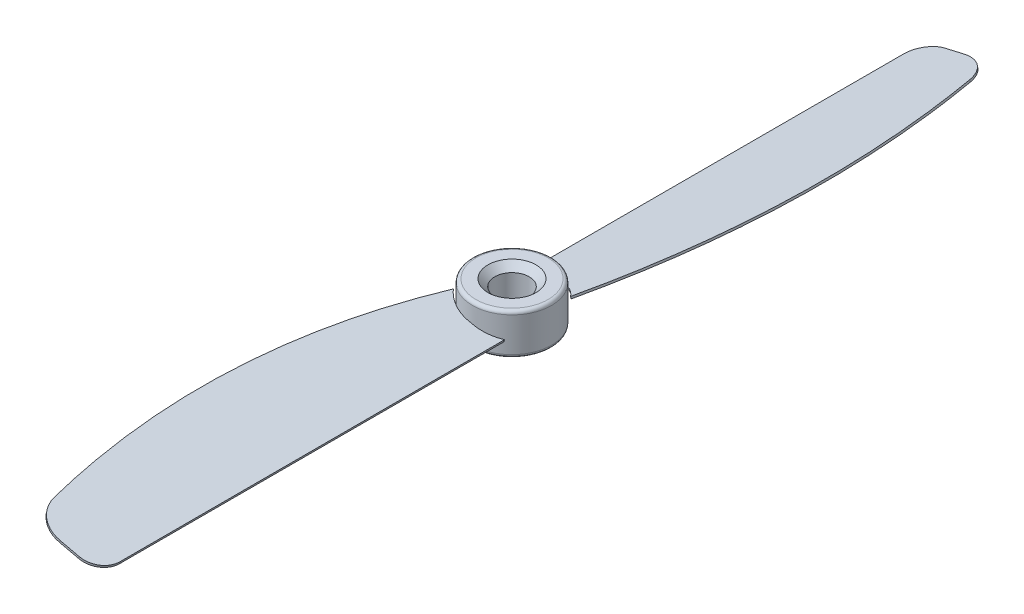
SolidWorks part; units mm, degrees
ref_plane "Front Plane" through (0, 0, 0) normal (0, 0, 1) x (1, 0, 0)
ref_plane "Top Plane" through (0, 0, 0) normal (0, 1, 0) x (1, 0, 0)
ref_plane "Right Plane" through (0, 0, 0) normal (1, 0, 0) x (0, 0, -1)
sketch "Sketch1" plane through (0, 0, 0) normal (0, 1, 0) x (1, 0, 0)
  circle A0 centre (0, 0) radius 5.75
  dimension "D1" = 11.5
extrude "Boss-Extrude1" add sketch "Sketch1" along normal mid plane 6
sketch "Sketch2" plane through (0, 0, 0) normal (0, 0, 1) x (1, 0, 0)
  line L0 (-5.75, 1.3275) -> (5.75, -1.3275) construction
  line L1 (-5.75, 3) -> (-5.75, -3) construction
  line L2 (5.75, -3) -> (5.75, 3) construction
  line L3 (-5.75, -3) -> (5.75, -3) construction
  dimension "D1" = 13
ref_plane "Plane1" through (0, 0, 0) normal (-0.225, -0.9744, 0) x (0.9744, -0.225, 0)
sketch "Sketch3" plane through (0, 0, 0) normal (-0.225, -0.9744, 0) x (0.9744, -0.225, 0)
  line L0 (3.5434, 3.7843) -> (3.5434, 60.5)
  line L1 (0.5434, 63.5) -> (-2.3272, 63.5)
  arc A0 (-7.21, 59.5763) -> (-2.3272, 63.5) centre (-2.3272, 58.5) cw
  arc A1 (3.5434, 60.5) -> (0.5434, 63.5) centre (0.5434, 60.5) ccw
  ellipse E0 centre (-0.6749, 0) end of major axis (-0.6749, 5.75) minor radius 5.6026
  ellipse E1 centre (-0.6749, 0) end of major axis (-0.6749, 5.75) minor radius 5.6026 construction
  spline S0 degree 3 poles (-4.8931, 3.7843) (-10.6556, 21.7345) (-11.4397, 40.3868) (-7.21, 59.5763) knots 0 0 0 0 0.936317 0.936317 0.936317 0.936317
  point P16 (0, 0)
  dimension "D2" = 5
  dimension "D3" = 3
  dimension "D1" = 63.5
extrude "Boss-Extrude2" add sketch "Sketch3" along normal mid plane 0.3 contours S0 E0 L0 A1 L1 A0
pattern_circular "CirPattern1" count 2 over 360 about axis through (0, 3, 0) along (0, -1, 0) of "Boss-Extrude2"
sketch "Sketch4" plane through (0, 3, 0) normal (0, 1, 0) x (1, 0, 0)
  circle A0 centre (0, 0) radius 2.5
extrude "Cut-Extrude1" cut sketch "Sketch4" against normal through all
fillet "Fillet1" radius 0.5 2 edges at (0, -3, 5.75) (0, 3, 5.75)
chamfer "Chamfer1" distance 1 angle 45 2 edges at (0, 3, 2.5) (0, -3, 2.5)
